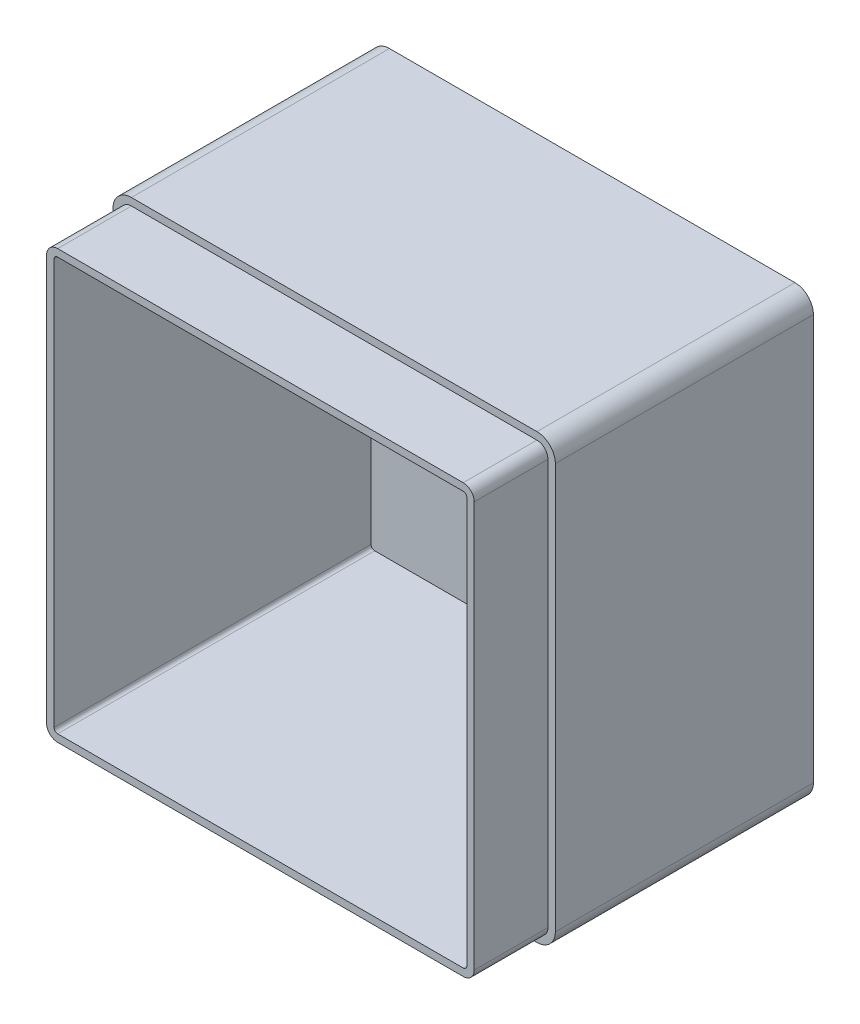
SolidWorks part; units mm, degrees
ref_plane "Front Plane" through (0, 0, 0) normal (0, 0, 1) x (1, 0, 0)
ref_plane "Top Plane" through (0, 0, 0) normal (0, 1, 0) x (1, 0, 0)
ref_plane "Right Plane" through (0, 0, 0) normal (1, 0, 0) x (0, 0, -1)
sketch "Sketch1" plane through (0, 0, 0) normal (0, 0, 1) x (1, 0, 0)
  line L1 (0, 0) -> (120, 0)
  line L2 (0, 0) -> (0, 120)
  line L3 (0, 120) -> (120, 120)
  line L4 (120, 0) -> (120, 120)
  dimension "D1" = 120
  dimension "D2" = 120
extrude "Boss-Extrude1" add sketch "Sketch1" along normal blind 90
fillet "Fillet1" radius 5 4 edges at (120, 120, 45) (0, 120, 45) (120, 0, 45) (0, 0, 45)
shell "Shell1" thickness 4
sketch "Sketch8" plane through (0, 0, 90) normal (0, 0, 1) x (1, 0, 0)
  line L4 (120, 5) -> (120, 115)
  line L5 (115, 120) -> (5, 120)
  line L6 (0, 115) -> (0, 5)
  line L7 (5, 0) -> (115, 0)
  line L8 (120, 5) -> (120, 115)
  line L9 (115, 120) -> (5, 120)
  line L10 (0, 115) -> (0, 5)
  line L11 (5, 0) -> (115, 0)
  line L16 (118, 5) -> (118, 115)
  line L17 (115, 118) -> (5, 118)
  line L18 (2, 115) -> (2, 5)
  line L19 (5, 2) -> (115, 2)
  line L20 (118, 5) -> (118, 115)
  line L21 (115, 118) -> (5, 118)
  line L22 (2, 115) -> (2, 5)
  line L23 (5, 2) -> (115, 2)
  arc A4 (120, 115) -> (115, 120) centre (115, 115) ccw
  arc A5 (5, 120) -> (0, 115) centre (5, 115) ccw
  arc A6 (0, 5) -> (5, 0) centre (5, 5) ccw
  arc A7 (115, 0) -> (120, 5) centre (115, 5) ccw
  arc A8 (120, 115) -> (115, 120) centre (115, 115) ccw
  arc A9 (5, 120) -> (0, 115) centre (5, 115) ccw
  arc A10 (0, 5) -> (5, 0) centre (5, 5) ccw
  arc A11 (115, 0) -> (120, 5) centre (115, 5) ccw
  arc A16 (118, 115) -> (115, 118) centre (115, 115) ccw
  arc A17 (5, 118) -> (2, 115) centre (5, 115) ccw
  arc A18 (2, 5) -> (5, 2) centre (5, 5) ccw
  arc A19 (115, 2) -> (118, 5) centre (115, 5) ccw
  arc A20 (118, 115) -> (115, 118) centre (115, 115) ccw
  arc A21 (5, 118) -> (2, 115) centre (5, 115) ccw
  arc A22 (2, 5) -> (5, 2) centre (5, 5) ccw
  arc A23 (115, 2) -> (118, 5) centre (115, 5) ccw
  dimension "D1" = 0
  dimension "D2" = 2
extrude "Cut-Extrude2" cut sketch "Sketch8" against normal blind 20
